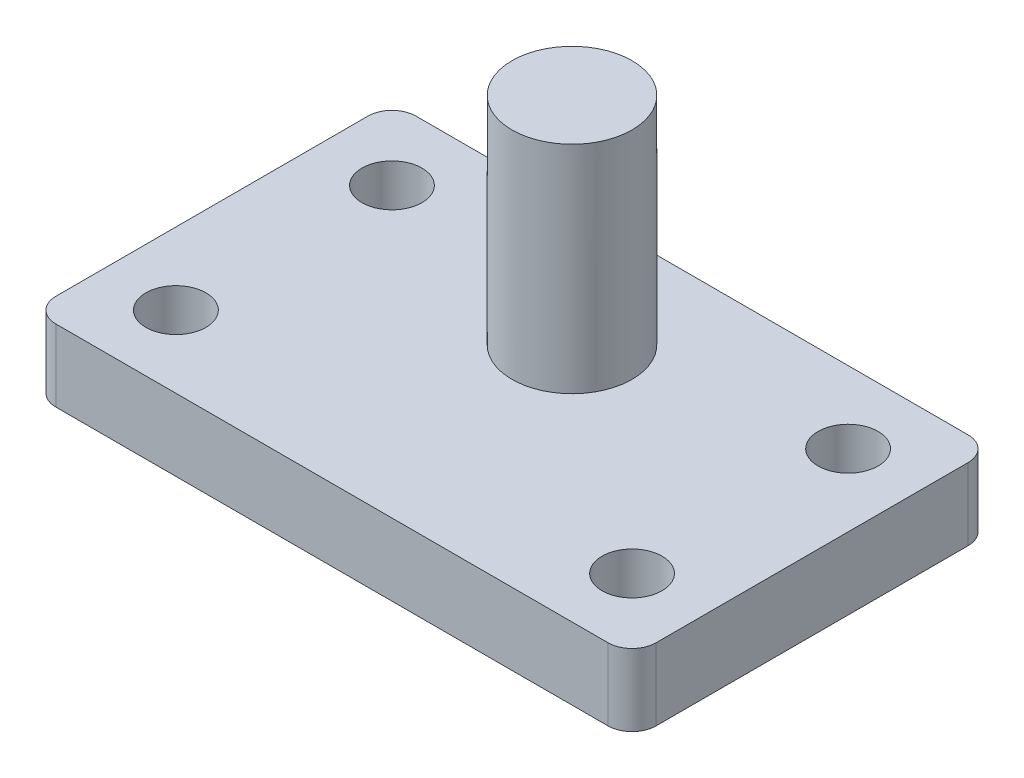
SolidWorks part; units mm, degrees
ref_plane "Front Plane" through (0, 0, 0) normal (0, 0, 1) x (1, 0, 0)
ref_plane "Top Plane" through (0, 0, 0) normal (0, 1, 0) x (1, 0, 0)
ref_plane "Right Plane" through (0, 0, 0) normal (1, 0, 0) x (0, 0, -1)
sketch "Sketch1" plane through (0, 0, 0) normal (0, 1, 0) x (1, 0, 0)
  line L1 (115, -75) -> (-115, -75)
  line L2 (125, -65) -> (125, 65)
  line L3 (115, 75) -> (-115, 75)
  line L4 (-125, -65) -> (-125, 65)
  line L5 (125, -75) -> (-125, 75) construction
  line L6 (125, 75) -> (-125, -75) construction
  arc A0 (-115, -75) -> (-125, -65) centre (-115, -65) cw
  arc A1 (125, 65) -> (115, 75) centre (115, 65) ccw
  arc A2 (115, -75) -> (125, -65) centre (115, -65) ccw
  arc A3 (-115, 75) -> (-125, 65) centre (-115, 65) ccw
  point P0 (0, 0)
  dimension "D3" = 10
  dimension "D1" = 250
  dimension "D2" = 150
extrude "Boss-Extrude1" add sketch "Sketch1" along normal blind 30
sketch "Sketch2" plane through (0, 30, 0) normal (0, 1, 0) x (1, 0, 0)
  line L0 (115, 75) -> (-115, 75) construction
  circle A0 centre (0, 25) radius 25
  dimension "D1" = 50
  dimension "D2" = 50
extrude "Boss-Extrude2" add sketch "Sketch2" along normal blind 90
sketch "Sketch3" plane through (0, 30, 0) normal (0, 1, 0) x (1, 0, 0)
  line L0 (115, 75) -> (-115, 75) construction
  line L2 (125, -65) -> (125, 65) construction
  line L3 (-125, 65) -> (-125, -65) construction
  line L4 (0, 0) -> (53.766, 0) construction
  circle A0 centre (-95, 45) radius 12.5
  circle A1 centre (95, 45) radius 12.5
  circle A2 centre (95, -45) radius 12.5
  circle A3 centre (-95, -45) radius 12.5
  dimension "D1" = 25
  dimension "D2" = 25
  dimension "D3" = 30
  dimension "D4" = 30
  dimension "D5" = 30
  dimension "D6" = 30
extrude "Cut-Extrude1" cut sketch "Sketch3" against normal through all
